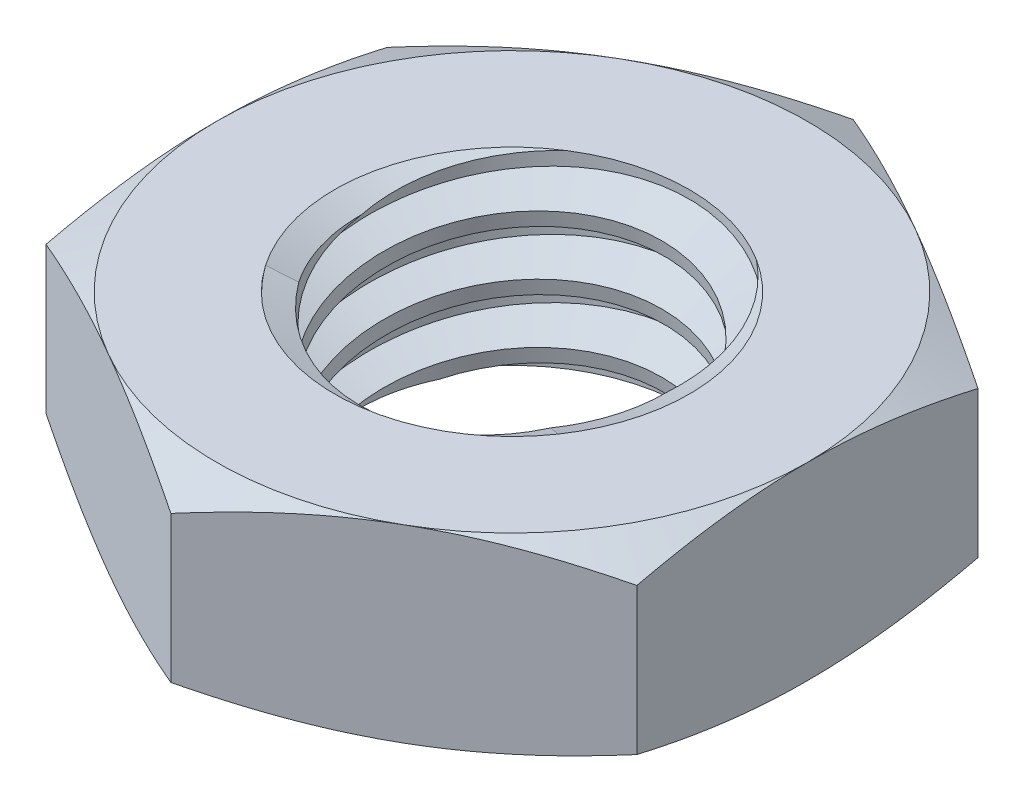
SolidWorks part; units mm, degrees
ref_plane "Front" through (0, 0, 0) normal (0, 0, 1) x (1, 0, 0)
ref_plane "Top" through (0, 0, 0) normal (0, 1, 0) x (1, 0, 0)
ref_plane "Right" through (0, 0, 0) normal (1, 0, 0) x (0, 0, -1)
sketch "Sketch1" plane through (0, 0, 0) normal (0, 1, 0) x (1, 0, 0)
  line L1 (0, 5.7735) -> (-5, 2.8868)
  line L2 (-5, 2.8868) -> (-5, -2.8868)
  line L3 (-5, -2.8868) -> (0, -5.7735)
  line L4 (0, -5.7735) -> (5, -2.8868)
  line L5 (5, -2.8868) -> (5, 2.8868)
  line L6 (5, 2.8868) -> (0, 5.7735)
  circle A0 centre (0, 0) radius 5 construction
  dimension "Hex Flats" = 10
extrude "Extrude1" add sketch "Sketch1" along normal mid plane 3.2
sketch "Sketch2" plane through (0, 0, 0) normal (1, 0, 0) x (0, 0, -1)
  line L0 (-3, -1.6) -> (-3, 1.6) construction
  line L1 (0, -1.6) -> (3, -1.6)
  line L2 (0, -1.6) -> (0, 1.6)
  line L3 (0, 1.6) -> (3, 1.6)
  line L4 (3, -1.6) -> (3, 1.6)
  line L5 (-2.8868, 1.6) -> (2.8868, 1.6) construction
  line L6 (-2.8868, -1.6) -> (2.8868, -1.6) construction
  line L7 (0, -4.6) -> (0, -1.6) construction
  dimension "Thread Dia" = 6
revolve "Revolve1" add sketch "Sketch2" angle 360 about L7
sketch "Sketch3" plane through (0, 0, 0) normal (1, 0, 0) x (0, 0, -1)
  line L0 (3, 1.6) -> (-3, 1.6) construction
  line L1 (-3, 1.6) -> (-3, 0.6) construction
  line L2 (-3, 0.6) -> (3, 1.6) construction
  line L3 (3, 1.6) -> (3.0205, 1.4767) construction
  line L4 (3.0205, 1.4767) -> (3.1644, 0.6136)
  line L5 (3.1644, 0.6136) -> (2.5791, 0.8329)
  line L6 (2.5791, 0.8329) -> (2.538, 1.0795)
  line L7 (2.538, 1.0795) -> (3.0205, 1.4767)
  line L8 (2.5586, 0.9562) -> (3.0925, 1.0452) construction
  line L9 (3, 1.6) -> (3, 1.0297) construction
  line L10 (3, 1.0297) -> (-3, 0.0297) construction
  line L11 (-3, 0.0297) -> (-3, 0.6) construction
  line L12 (-0.1784, 1.6) -> (0.1784, -0.5405) construction
  line L13 (-3, -1.6) -> (-3, 1.6) construction
  line L14 (0, 1.6) -> (3, 1.6) construction
  line L15 (3, -1.6) -> (3, 1.6) construction
  line L16 (0, 0) -> (0, 1.6) construction
  line L17 (-3.0205, 1.4767) -> (-3.1644, 0.6136) construction
  line L18 (-2.538, 1.0795) -> (-3.0205, 1.4767) construction
  line L19 (-2.5791, 0.8329) -> (-2.538, 1.0795) construction
  line L20 (-3.1644, 0.6136) -> (-2.5791, 0.8329) construction
  line L21 (0.1784, 1.6) -> (-0.1784, -0.5405) construction
  point P13 (0, 0.5297)
  dimension "D1" = 0.125
  dimension "D2" = 0.25
  dimension "Thread Pitch" = 1
  dimension "D4" = 60
  dimension "D5" = 1
revolve "Cut-Revolve1" cut sketch "Sketch3" angle 360 about L12
pattern_linear "LPattern1" count 3 spacing 1 along (0, -1, 0) count 2 spacing 1 along (0, 1, 0) of "Cut-Revolve1"
sketch "Sketch4" plane through (0, 0, 0) normal (1, 0, 0) x (0, 0, -1)
  line L0 (0, 1.6) -> (3, 1.6)
  line L1 (3, 1.6) -> (2.538, 1.3846)
  line L2 (2.538, 1.3846) -> (2.538, -1.3846)
  line L3 (2.538, -1.3846) -> (3, -1.6)
  line L4 (3, -1.6) -> (0, -1.6)
  line L5 (0, -1.6) -> (0, 1.6)
  line L6 (3, -1.6) -> (3, 1.6) construction
  line L7 (0, 1.6) -> (3, 1.6) construction
  line L8 (0, -1.6) -> (3, -1.6) construction
  line L9 (0, -1.6) -> (0, 1.6) construction
  line L10 (0, 1.6) -> (0, 2.1097) construction
  dimension "D1" = 25
revolve "Cut-Revolve2" cut sketch "Sketch4" angle 360 about L10
combine bodies "Combine1" operation type subtract main body 112 bodies to subtract 111
sketch "Sketch5" plane through (0, 0, 0) normal (1, 0, 0) x (0, 0, -1)
  line L0 (0, -1.6) -> (5, -1.6)
  line L1 (5, -1.6) -> (5.7735, -1.2393)
  line L2 (5.7735, -1.2393) -> (5.7735, 1.2393)
  line L3 (5.7735, 1.2393) -> (5, 1.6)
  line L4 (0, 1.6) -> (0, 2.87)
  line L5 (0, 2.87) -> (7.0435, 2.87)
  line L6 (7.0435, 2.87) -> (7.0435, -2.87)
  line L7 (7.0435, -2.87) -> (0, -2.87)
  line L8 (0, -2.87) -> (0, -1.6)
  line L9 (5, 1.6) -> (5, -1.6) construction
  line L11 (0, -1.6) -> (3, -1.6) construction
  line L12 (5, 1.6) -> (0, 1.6)
  line L13 (5.7735, 0) -> (7.0435, 0) construction
  line L14 (5.7735, 1.6) -> (5.7735, -1.6) construction
  line L15 (0, -1.6) -> (0, 1.6) construction
  line L17 (0, 0) -> (5, 0) construction
  line L22 (0, 1.6) -> (3, 1.6) construction
  dimension "D1" = 25
  dimension "D2" = 1.27
  dimension "D3" = 3.2
revolve "Cut-Revolve3" cut sketch "Sketch5" angle 360 about L15
equation "\"D1@Sketch3\"=\"Thread Pitch@Sketch3\"/8"
equation "\"D2@Sketch3\"=\"Thread Pitch@Sketch3\"/4"
equation "\"D5@Sketch3\"=\"Thread Pitch@Sketch3\""
equation "\"D4@LPattern1\"=\"Thread Pitch@Sketch3\""
equation "\"D3@LPattern1\"=\"Thread Pitch@Sketch3\""
equation "\"D1@LPattern1\"=\"Height@Extrude1\"/\"Thread Pitch@Sketch3\""
